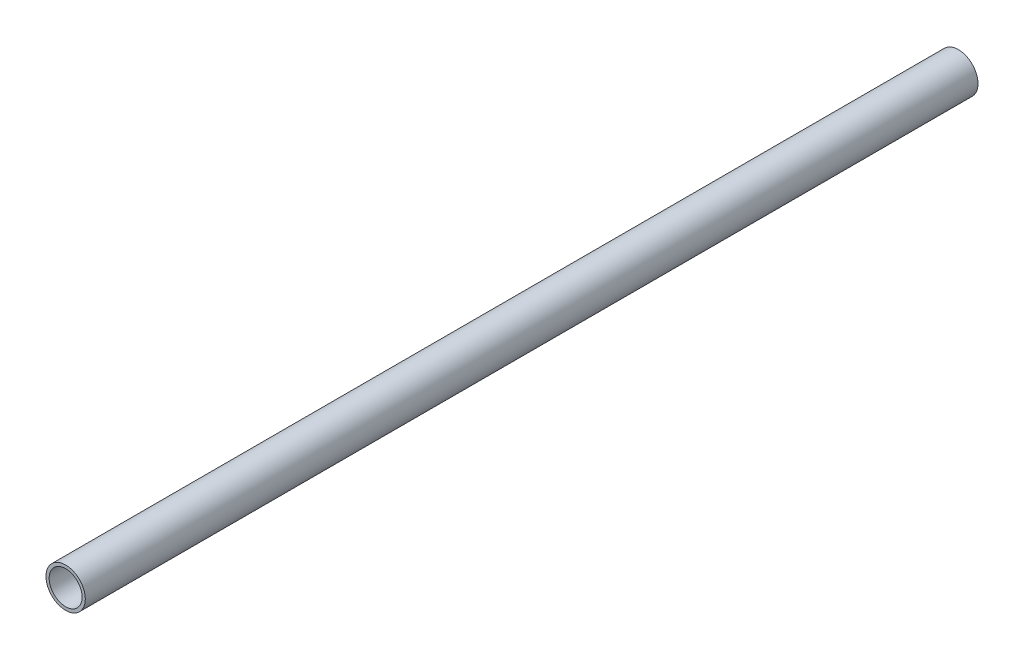
SolidWorks part; units mm, degrees
material "carbon"
ref_plane "Płaszczyzna XY" through (0, 0, 0) normal (0, 0, 1) x (1, 0, 0)
ref_plane "Płaszczyzna XZ" through (0, 0, 0) normal (0, 1, 0) x (1, 0, 0)
ref_plane "Płaszczyzna YZ" through (0, 0, 0) normal (1, 0, 0) x (0, 0, -1)
sketch "Szkic1" plane through (0, 0, 0) normal (0, 0, 1) x (1, 0, 0)
  circle A0 centre (0, 0) radius 7
  circle A1 centre (0, 0) radius 8.35
  dimension "D1" = 14
  dimension "D2" = 16.7
extrude "Dodanie-wyciągnięcie1" add sketch "Szkic1" along normal blind 341 and the other way blind 38
